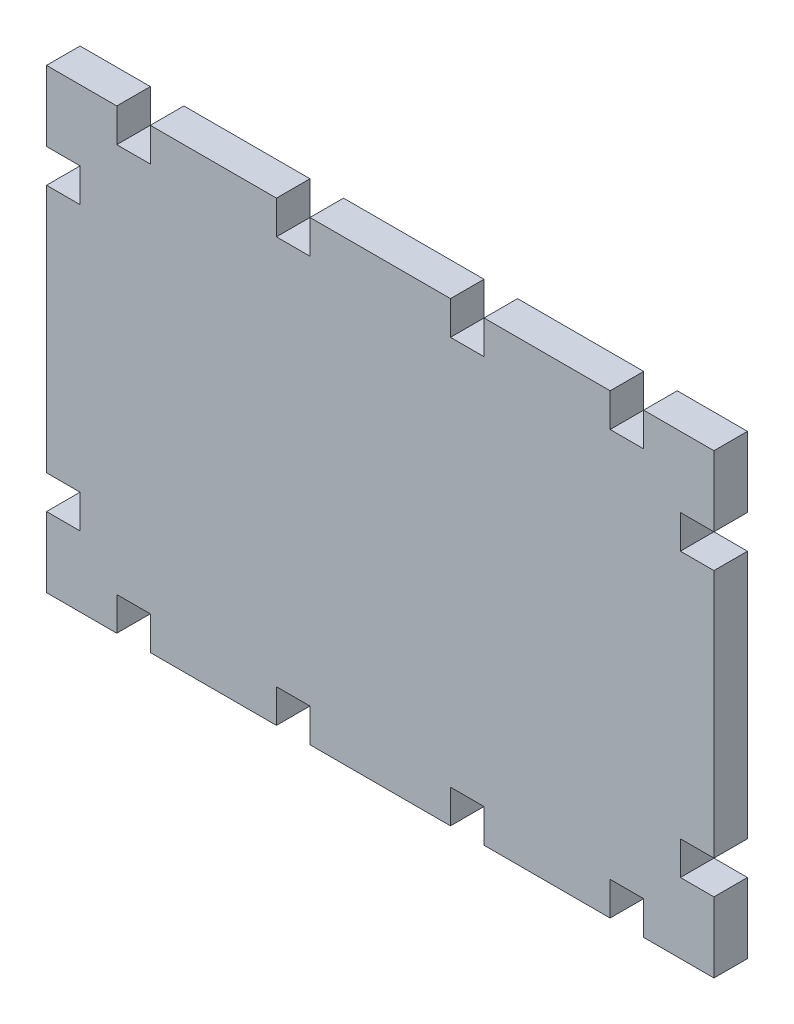
SolidWorks part; units mm, degrees
ref_plane "Front Plane" through (0, 0, 0) normal (0, 0, 1) x (1, 0, 0)
ref_plane "Top Plane" through (0, 0, 0) normal (0, 1, 0) x (1, 0, 0)
ref_plane "Right Plane" through (0, 0, 0) normal (1, 0, 0) x (0, 0, -1)
sketch "Sketch3" plane through (0, 0, 0) normal (0, 0, 1) x (1, 0, 0)
  line L29 (0, 0) -> (0, 32.5) construction
  line L30 (0, 0) -> (95, 0) construction
  line L31 (0, 0) -> (47.5, 0) construction
  line L32 (0, 0) -> (10, 0) construction
  line L33 (10, 0) -> (10, 4.7752)
  line L34 (10, 4.7752) -> (14.7752, 4.7752)
  line L35 (14.7752, 4.7752) -> (14.7752, 0)
  line L36 (47.5, 0) -> (47.5, 4.7752) construction
  line L37 (47.5, 4.7752) -> (37.5, 4.7752) construction
  line L38 (37.5, 4.7752) -> (37.5, 0)
  line L39 (37.5, 4.7752) -> (32.7248, 4.7752)
  line L40 (32.7248, 4.7752) -> (32.7248, 0)
  line L41 (14.7752, 0) -> (32.7248, 0)
  line L42 (10, 0) -> (0, 0)
  line L43 (37.5, 0) -> (47.5, 0)
  line L44 (57.5, 4.7752) -> (57.5, 0)
  line L45 (62.2752, 4.7752) -> (62.2752, 0)
  line L46 (57.5, 4.7752) -> (62.2752, 4.7752)
  line L47 (80.2248, 4.7752) -> (80.2248, 0)
  line L48 (85, 0) -> (85, 4.7752)
  line L49 (85, 4.7752) -> (80.2248, 4.7752)
  line L50 (47.5, 0) -> (57.5, 0)
  line L51 (62.2752, 0) -> (80.2248, 0)
  line L52 (85, 0) -> (95, 0)
  line L53 (0, 32.5) -> (95, 32.5) construction
  line L54 (85, 65) -> (85, 60.2248)
  line L55 (80.2248, 60.2248) -> (80.2248, 65)
  line L56 (85, 60.2248) -> (80.2248, 60.2248)
  line L57 (62.2752, 60.2248) -> (62.2752, 65)
  line L58 (57.5, 60.2248) -> (57.5, 65)
  line L59 (57.5, 60.2248) -> (62.2752, 60.2248)
  line L60 (37.5, 60.2248) -> (37.5, 65)
  line L61 (32.7248, 60.2248) -> (32.7248, 65)
  line L62 (37.5, 60.2248) -> (32.7248, 60.2248)
  line L63 (14.7752, 60.2248) -> (14.7752, 65)
  line L64 (10, 65) -> (10, 60.2248)
  line L65 (10, 60.2248) -> (14.7752, 60.2248)
  line L66 (10, 65) -> (0, 65)
  line L67 (0, 65) -> (0, 0) construction
  line L68 (14.7752, 65) -> (32.7248, 65)
  line L69 (37.5, 65) -> (57.5, 65)
  line L70 (62.2752, 65) -> (80.2248, 65)
  line L71 (85, 65) -> (95, 65)
  line L72 (95, 65) -> (95, 0) construction
  line L73 (95, 65) -> (95, 55)
  line L74 (95, 55) -> (90.2248, 55)
  line L75 (90.2248, 55) -> (90.2248, 50.2248)
  line L76 (90.2248, 50.2248) -> (95, 50.2248)
  line L77 (95, 50.2248) -> (95, 32.5)
  line L78 (90.2248, 14.7752) -> (95, 14.7752)
  line L79 (90.2248, 10) -> (90.2248, 14.7752)
  line L80 (95, 10) -> (90.2248, 10)
  line L81 (95, 32.5) -> (95, 14.7752)
  line L82 (95, 10) -> (95, 0)
  line L83 (0, 32.5) -> (47.5, 32.5) construction
  line L84 (47.5, 32.5) -> (47.5, 0) construction
  line L85 (0, 10) -> (4.7752, 10)
  line L86 (4.7752, 10) -> (4.7752, 14.7752)
  line L87 (4.7752, 14.7752) -> (0, 14.7752)
  line L88 (4.7752, 50.2248) -> (0, 50.2248)
  line L89 (0, 55) -> (4.7752, 55)
  line L90 (4.7752, 55) -> (4.7752, 50.2248)
  line L91 (0, 55) -> (0, 65)
  line L92 (0, 10) -> (0, 0)
  line L93 (0, 50.2248) -> (0, 14.7752)
  dimension "D1" = 95
  dimension "D2" = 47.5
  dimension "D3" = 10
  dimension "D4" = 4.7752
  dimension "D5" = 4.7752
  dimension "D7" = 10
  dimension "D8" = 32.5
  dimension "D9" = 4.7752
  dimension "D10" = 10
  dimension "D6" = 4.7752
  dimension "D11" = 10
  dimension "D12" = 4.7752
  dimension "D13" = 4.7752
extrude "Boss-Extrude1" add sketch "Sketch3" against normal blind 4.7752
